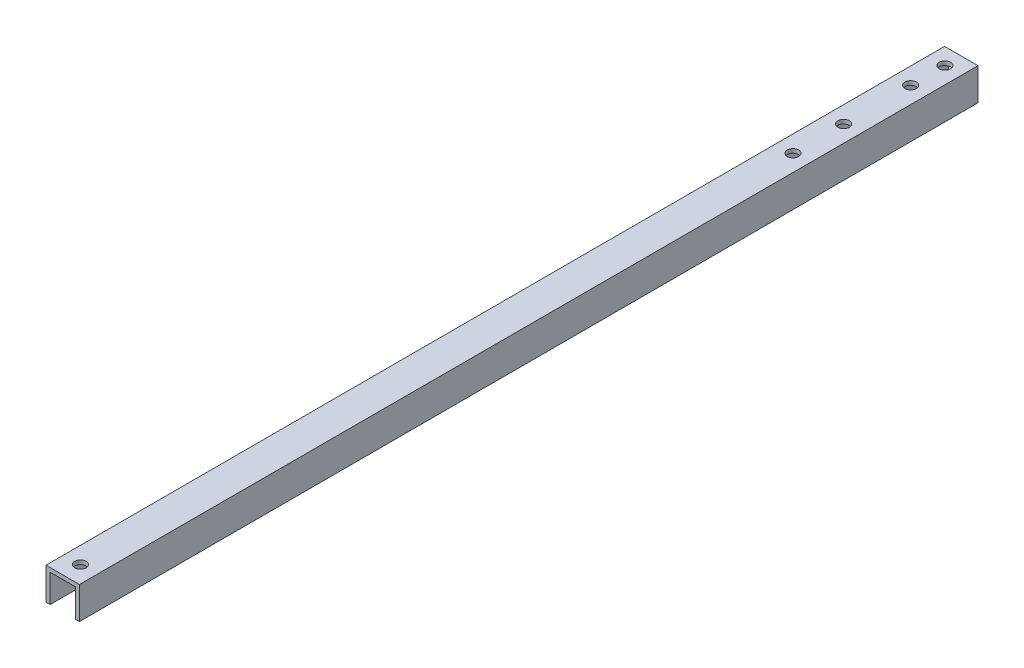
SolidWorks part; units mm, degrees
ref_plane "Front Plane" through (0, 0, 0) normal (0, 0, 1) x (1, 0, 0)
ref_plane "Top Plane" through (0, 0, 0) normal (0, 1, 0) x (1, 0, 0)
ref_plane "Right Plane" through (0, 0, 0) normal (1, 0, 0) x (0, 0, -1)
sketch "Sketch1" plane through (0, 0, 0) normal (0, 0, 1) x (1, 0, 0)
  line L0 (0, 0) -> (0, -1.5875) construction
  line L1 (-6.604, 0) -> (6.604, 0)
  line L2 (6.604, 0) -> (6.604, -12.7)
  line L3 (6.604, -12.7) -> (5.0165, -12.7)
  line L4 (5.0165, -12.7) -> (5.0165, -1.5875)
  line L5 (5.0165, -1.5875) -> (-5.0165, -1.5875)
  line L6 (-5.0165, -12.7) -> (-5.0165, -1.5875)
  line L7 (-6.604, -12.7) -> (-5.0165, -12.7)
  line L8 (-6.604, 0) -> (-6.604, -12.7)
  dimension "D1" = 12.7
  dimension "D2" = 1.5875
  dimension "D3" = 13.208
extrude "Boss-Extrude1" add sketch "Sketch1" against normal blind 355
hole_wizard "M4 Clearance Hole2" positions "Sketch4" profile "Sketch5" hole size "M4" standard "ANSI Metric" end condition through all
sketch "Sketch4" plane through (0, 0, 0) normal (0, 1, 0) x (1, 0, 0)
  line L0 (6.604, 0) -> (-6.604, 0) construction
  point P9 (0, 7)
  point P16 (0, 348.5)
  point P25 (0, 308.5)
  point P29 (0, 335)
  point P33 (0, 288.5)
  point P36 (0, 0)
  point P37 (0, 0)
  dimension "D3" = 341.5
  dimension "D1" = 7
  dimension "D4" = 40
  dimension "D5" = 13.5
  dimension "D6" = 20
sketch "Sketch5" plane through (0, 0, -288.5) normal (1, 0, 0) x (0, 0, 1)
  line L0 (0, 0) -> (0, 12.7)
  line L1 (0, 12.7) -> (2.25, 12.7)
  line L2 (2.25, 12.7) -> (2.25, 0)
  line L5 (2.25, 0) -> (0, 0)
  line L11 (0, -6.35) -> (0, 107.95) construction
  dimension "Thru Hole Dia." = 4.5
  dimension "Thru Hole Depth" = 12.7
